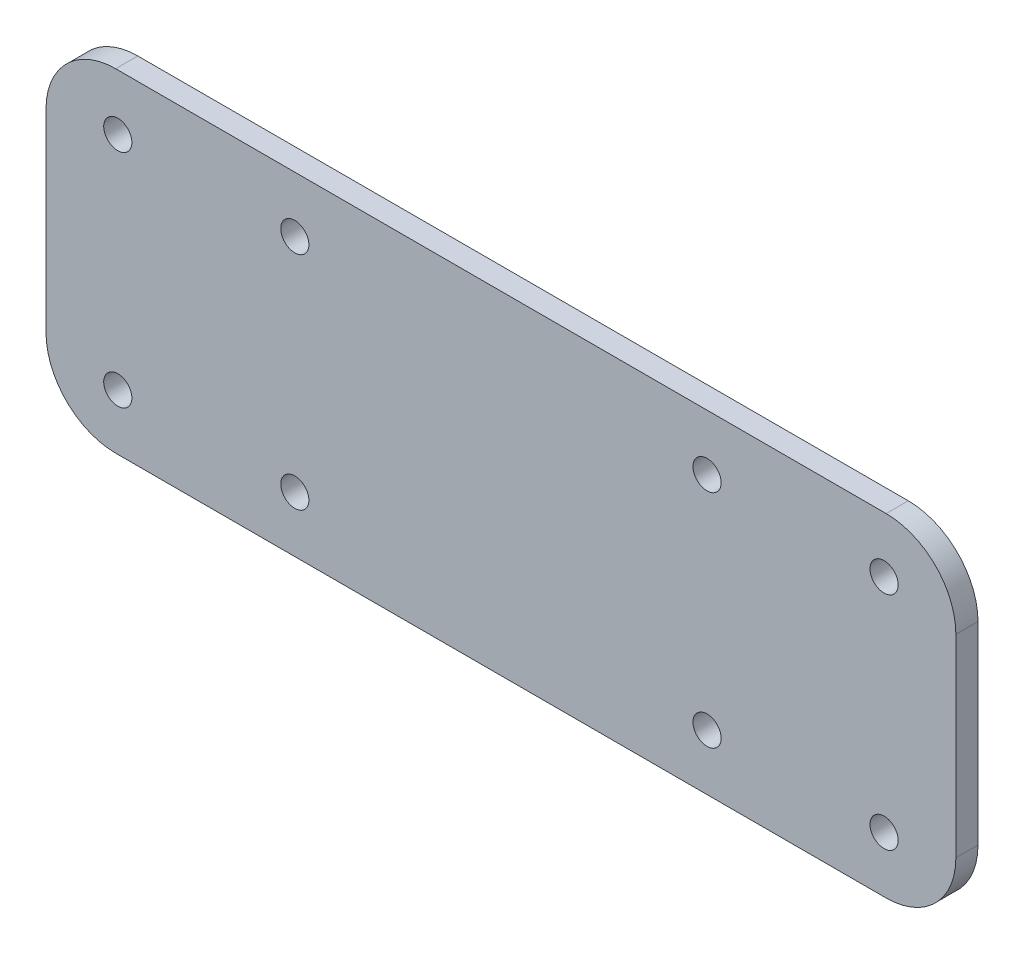
SolidWorks part; units mm, degrees
ref_plane "Front Plane" through (0, 0, 0) normal (0, 0, 1) x (1, 0, 0)
ref_plane "Top Plane" through (0, 0, 0) normal (0, 1, 0) x (1, 0, 0)
ref_plane "Right Plane" through (0, 0, 0) normal (1, 0, 0) x (0, 0, -1)
sketch "Sketch1" plane through (0, 0, 0) normal (0, 0, 1) x (1, 0, 0)
  line L0 (39.3854, -40.0501) -> (39.3854, -52.4111) construction
  line L1 (165.9345, -56.675) -> (165.9345, -42.05) construction
  line L2 (157.3152, -8.05) -> (165.9345, -16.6693)
  line L3 (157.3152, 245.3495) -> (165.9345, 253.9688)
  line L4 (39.3854, -40.0501) -> (39.3854, -52.4111)
  line L5 (165.9345, -56.675) -> (165.9345, -42.05)
  line L6 (165.9345, 245.3495) -> (39.3854, 245.3495)
  line L7 (165.9345, 279.3495) -> (165.9345, 245.3495)
  line L8 (39.3854, -52.4111) -> (165.9345, -56.675)
  line L9 (39.3854, 289.7105) -> (165.9345, 293.9745)
  line L10 (39.3854, -40.0501) -> (39.3854, -16.6693)
  line L11 (165.9345, -42.05) -> (165.9345, -16.6693)
  line L12 (157.3152, -8.05) -> (48.0047, -8.0501)
  line L13 (42.1433, 0) -> (42.1433, 237.2995) construction
  line L14 (42.1433, 118.6497) -> (215.0534, 118.6497) construction
  line L15 (165.9345, 293.9745) -> (165.9345, 279.3495)
  line L16 (39.3854, 277.3495) -> (39.3854, 245.3495)
  line L17 (39.3854, 277.3495) -> (39.3854, 289.7105)
  line L18 (102.66, -54.5431) -> (102.66, 291.8425) construction
  line L19 (102.66, 291.8425) -> (73.0854, -499321.8282) construction
  line L20 (39.3854, -16.6693) -> (89.96, 33.9052)
  line L21 (89.96, -8.05) -> (115.36, -8.05)
  line L22 (89.96, -8.05) -> (89.96, 245.3495)
  line L23 (89.96, 245.3495) -> (115.36, 245.3495)
  line L24 (115.36, -8.05) -> (115.36, 245.3495)
  line L25 (89.96, -8.05) -> (115.36, 245.3495) construction
  line L26 (89.96, 245.3495) -> (115.36, -8.05) construction
  line L27 (115.36, 33.9052) -> (157.3152, -8.05)
  line L28 (115.36, 203.3943) -> (157.3152, 245.3495)
  line L29 (39.3854, 253.9688) -> (89.96, 203.3943)
  arc A0 (157.6345, 249.9303) -> (157.6345, 253.9689) centre (157.6345, 251.9496) cw
  arc A1 (157.6345, 253.9689) -> (157.6345, 249.9303) centre (157.6345, 251.9496) cw
  arc A2 (73.0854, 249.9303) -> (73.0854, 253.9689) centre (73.0854, 251.9496) ccw
  arc A3 (73.0854, 253.9689) -> (73.0854, 249.9303) centre (73.0854, 251.9496) ccw
  arc A4 (73.0854, 249.9303) -> (73.0854, 253.9689) centre (73.0854, 251.9496) ccw
  arc A5 (73.0854, 253.9689) -> (73.0854, 249.9303) centre (73.0854, 251.9496) ccw
  arc A6 (47.6854, 249.9303) -> (47.6854, 253.9689) centre (47.6854, 251.9496) cw
  arc A7 (47.6854, 253.9689) -> (47.6854, 249.9303) centre (47.6854, 251.9496) cw
  arc A10 (47.6854, 281.6802) -> (47.6854, 285.7188) centre (47.6854, 283.6995) cw
  arc A11 (47.6854, 285.7188) -> (47.6854, 281.6802) centre (47.6854, 283.6995) cw
  arc A14 (157.6345, -48.4194) -> (157.6345, -44.3807) centre (157.6345, -46.4001) ccw
  arc A15 (157.6345, -44.3807) -> (157.6345, -48.4194) centre (157.6345, -46.4001) ccw
  arc A16 (157.6345, -48.4194) -> (157.6345, -44.3807) centre (157.6345, -46.4001) ccw
  arc A17 (157.6345, -44.3807) -> (157.6345, -48.4194) centre (157.6345, -46.4001) ccw
  arc A18 (73.0854, 281.6802) -> (73.0854, 285.7188) centre (73.0854, 283.6995) cw
  arc A19 (73.0854, 285.7188) -> (73.0854, 281.6802) centre (73.0854, 283.6995) cw
  arc A22 (157.6345, -16.6693) -> (157.6345, -12.6307) centre (157.6345, -14.65) ccw
  arc A23 (157.6345, -12.6307) -> (157.6345, -16.6693) centre (157.6345, -14.65) ccw
  arc A24 (157.6345, -16.6693) -> (157.6345, -12.6307) centre (157.6345, -14.65) ccw
  arc A25 (157.6345, -12.6307) -> (157.6345, -16.6693) centre (157.6345, -14.65) ccw
  arc A26 (73.0854, -16.6693) -> (73.0854, -12.6307) centre (73.0854, -14.65) ccw
  arc A27 (73.0854, -12.6307) -> (73.0854, -16.6693) centre (73.0854, -14.65) ccw
  arc A28 (73.0854, -16.6693) -> (73.0854, -12.6307) centre (73.0854, -14.65) ccw
  arc A29 (73.0854, -12.6307) -> (73.0854, -16.6693) centre (73.0854, -14.65) ccw
  arc A30 (73.0854, 249.9303) -> (73.0854, 253.9689) centre (73.0854, 251.9496) cw
  arc A31 (73.0854, 253.9689) -> (73.0854, 249.9303) centre (73.0854, 251.9496) cw
  arc A34 (157.6345, 249.9303) -> (157.6345, 253.9689) centre (157.6345, 251.9496) ccw
  arc A35 (157.6345, 253.9689) -> (157.6345, 249.9303) centre (157.6345, 251.9496) ccw
  arc A36 (157.6345, 249.9303) -> (157.6345, 253.9689) centre (157.6345, 251.9496) ccw
  arc A37 (157.6345, 253.9689) -> (157.6345, 249.9303) centre (157.6345, 251.9496) ccw
  arc A38 (47.6854, 249.9303) -> (47.6854, 253.9689) centre (47.6854, 251.9496) ccw
  arc A39 (47.6854, 253.9689) -> (47.6854, 249.9303) centre (47.6854, 251.9496) ccw
  arc A40 (47.6854, 249.9303) -> (47.6854, 253.9689) centre (47.6854, 251.9496) ccw
  arc A41 (47.6854, 253.9689) -> (47.6854, 249.9303) centre (47.6854, 251.9496) ccw
  arc A42 (73.0854, -48.4194) -> (73.0854, -44.3807) centre (73.0854, -46.4001) ccw
  arc A43 (73.0854, -44.3807) -> (73.0854, -48.4194) centre (73.0854, -46.4001) ccw
  arc A44 (73.0854, -48.4194) -> (73.0854, -44.3807) centre (73.0854, -46.4001) ccw
  arc A45 (73.0854, -44.3807) -> (73.0854, -48.4194) centre (73.0854, -46.4001) ccw
  arc A46 (132.2345, 249.9303) -> (132.2345, 253.9689) centre (132.2345, 251.9496) ccw
  arc A47 (132.2345, 253.9689) -> (132.2345, 249.9303) centre (132.2345, 251.9496) ccw
  arc A48 (132.2345, 249.9303) -> (132.2345, 253.9689) centre (132.2345, 251.9496) ccw
  arc A49 (132.2345, 253.9689) -> (132.2345, 249.9303) centre (132.2345, 251.9496) ccw
  arc A50 (47.6854, -48.4194) -> (47.6854, -44.3808) centre (47.6854, -46.4001) ccw
  arc A51 (47.6854, -44.3808) -> (47.6854, -48.4194) centre (47.6854, -46.4001) ccw
  arc A52 (47.6854, -48.4194) -> (47.6854, -44.3808) centre (47.6854, -46.4001) ccw
  arc A53 (47.6854, -44.3808) -> (47.6854, -48.4194) centre (47.6854, -46.4001) ccw
  arc A54 (47.6854, -16.6693) -> (47.6854, -12.6307) centre (47.6854, -14.65) ccw
  arc A55 (47.6854, -12.6307) -> (47.6854, -16.6693) centre (47.6854, -14.65) ccw
  arc A56 (47.6854, -16.6693) -> (47.6854, -12.6307) centre (47.6854, -14.65) ccw
  arc A57 (47.6854, -12.6307) -> (47.6854, -16.6693) centre (47.6854, -14.65) ccw
  arc A58 (157.6345, 281.6802) -> (157.6345, 285.7188) centre (157.6345, 283.6995) cw
  arc A59 (157.6345, 285.7188) -> (157.6345, 281.6802) centre (157.6345, 283.6995) cw
  arc A62 (132.2345, -16.6693) -> (132.2345, -12.6307) centre (132.2345, -14.65) ccw
  arc A63 (132.2345, -12.6307) -> (132.2345, -16.6693) centre (132.2345, -14.65) ccw
  arc A64 (132.2345, -16.6693) -> (132.2345, -12.6307) centre (132.2345, -14.65) ccw
  arc A65 (132.2345, -12.6307) -> (132.2345, -16.6693) centre (132.2345, -14.65) ccw
  arc A66 (132.2345, -48.4194) -> (132.2345, -44.3808) centre (132.2345, -46.4001) ccw
  arc A67 (132.2345, -44.3808) -> (132.2345, -48.4194) centre (132.2345, -46.4001) ccw
  arc A68 (132.2345, -48.4194) -> (132.2345, -44.3808) centre (132.2345, -46.4001) ccw
  arc A69 (132.2345, -44.3808) -> (132.2345, -48.4194) centre (132.2345, -46.4001) ccw
  point P62 (102.66, 118.6497)
  dimension "D3" = 0
  dimension "D2" = 25.4
  dimension "D1" = 0
  dimension "D4" = 0
  dimension "D5" = 0
  dimension "D6" = 0
  dimension "D7" = 0
  dimension "D9" = 0
  dimension "D10" = 0
  dimension "D11" = 0
  dimension "D12" = 0
  dimension "D13" = 0
  dimension "D14" = 0
extrude "Boss-Extrude1" add sketch "Sketch1" along normal blind 3.175 contours L20 L10 L4 L8 L5 L11 L2 L12 A69 A68 A65 A64 A57 A56 A53 A52 A45 A44 A29 A28 A25 A24 A17 A16 | L27 L24 L12 | L12 L24 L6 L22 | L12 L22 L20 | L16 L29 L6 L3 L7 L15 L9 L17 A49 A48 A5 A4 A0 A1 A6 A7 A10 A11 A18 A19 A58 A59 | L24 L28 L6 | L6 L29 L22
sketch "Sketch2" plane through (0, 0, 3.175) normal (0, 0, 1) x (1, 0, 0)
  line L0 (165.9345, -56.675) -> (165.9345, -16.6693) construction
  line L1 (39.3854, -52.4111) -> (84.3854, -52.4111)
  line L2 (39.3854, -52.4111) -> (39.3854, -7.4111)
  line L3 (39.3854, -7.4111) -> (84.3854, -7.4111)
  line L4 (84.3854, -52.4111) -> (84.3854, -7.4111)
  line L5 (165.9345, -52.4111) -> (120.9345, -52.4111)
  line L6 (165.9345, -52.4111) -> (165.9345, -7.4111)
  line L7 (165.9345, -7.4111) -> (120.9345, -7.4111)
  line L8 (120.9345, -52.4111) -> (120.9345, -7.4111)
  line L9 (89.96, 118.6497) -> (115.36, 118.6497) construction
  line L10 (89.96, 33.9052) -> (89.96, 203.3943) construction
  line L11 (115.36, 33.9052) -> (115.36, 203.3943) construction
  line L12 (165.9345, 289.7105) -> (120.9345, 289.7105)
  line L13 (39.3854, 289.7105) -> (84.3854, 289.7105)
  line L14 (84.3854, -52.4111) -> (120.9345, -52.4111)
  line L15 (84.3854, 289.7105) -> (120.9345, 289.7105)
  line M9 (39.3854, -52.4111) -> (165.9345, -56.675)
  line M10 (165.9345, -56.675) -> (165.9345, -16.6693)
  line M14 (165.9345, 253.9688) -> (165.9345, 293.9745)
  line M15 (165.9345, 293.9745) -> (39.3854, 289.7105)
  dimension "D1" = 45
extrude "Cut-Extrude1" cut sketch "Sketch2" against normal blind 10 contours L14 L1 L5 M9 M10 | L13 L15 L12 M14 M15
sketch "Sketch3" plane through (0, 0, 3.175) normal (0, 0, 1) x (1, 0, 0)
  line L25 (37.3854, -15.8409) -> (37.3854, -54.4111)
  line L26 (37.3854, -54.4111) -> (167.9345, -54.4111)
  line L27 (167.9345, -54.4111) -> (167.9345, -15.8409)
  line L28 (167.9345, -15.8409) -> (117.36, 34.7337)
  line L29 (117.36, 34.7337) -> (117.36, 202.5658)
  line L30 (117.36, 202.5658) -> (167.9345, 253.1404)
  line L31 (167.9345, 253.1404) -> (167.9345, 291.7105)
  line L32 (167.9345, 291.7105) -> (37.3854, 291.7105)
  line L33 (37.3854, 291.7105) -> (37.3854, 253.1404)
  line L34 (37.3854, 253.1404) -> (87.96, 202.5658)
  line L35 (87.96, 202.5658) -> (87.96, 34.7337)
  line L36 (87.96, 34.7337) -> (37.3854, -15.8409)
  line L37 (37.3854, -15.8409) -> (37.3854, -54.4111)
  line L38 (37.3854, -54.4111) -> (167.9345, -54.4111)
  line L39 (167.9345, -54.4111) -> (167.9345, -15.8409)
  line L40 (167.9345, -15.8409) -> (117.36, 34.7337)
  line L41 (117.36, 34.7337) -> (117.36, 202.5658)
  line L42 (117.36, 202.5658) -> (167.9345, 253.1404)
  line L43 (167.9345, 253.1404) -> (167.9345, 291.7105)
  line L44 (167.9345, 291.7105) -> (37.3854, 291.7105)
  line L45 (37.3854, 291.7105) -> (37.3854, 253.1404)
  line L46 (37.3854, 253.1404) -> (87.96, 202.5658)
  line L47 (87.96, 202.5658) -> (87.96, 34.7337)
  line L48 (87.96, 34.7337) -> (37.3854, -15.8409)
  circle A1 centre (132.2345, -46.4001) radius 2.0193
  circle A2 centre (132.2345, -46.4001) radius 2.0193
  circle A3 centre (132.2345, -14.65) radius 2.0193
  circle A4 centre (132.2345, -14.65) radius 2.0193
  circle A5 centre (47.6854, -14.65) radius 2.0193
  circle A6 centre (47.6854, -14.65) radius 2.0193
  circle A7 centre (47.6854, -46.4001) radius 2.0193
  circle A8 centre (47.6854, -46.4001) radius 2.0193
  circle A9 centre (73.0854, -46.4001) radius 2.0193
  circle A10 centre (73.0854, -46.4001) radius 2.0193
  circle A11 centre (73.0854, -14.65) radius 2.0193
  circle A12 centre (73.0854, -14.65) radius 2.0193
  circle A13 centre (157.6345, -14.65) radius 2.0193
  circle A14 centre (157.6345, -14.65) radius 2.0193
  circle A15 centre (157.6345, -46.4001) radius 2.0193
  circle A16 centre (157.6345, -46.4001) radius 2.0193
  circle A17 centre (132.2345, 251.9496) radius 2.0193
  circle A18 centre (132.2345, 251.9496) radius 2.0193
  circle A19 centre (73.0854, 251.9496) radius 2.0193
  circle A20 centre (73.0854, 251.9496) radius 2.0193
  circle A21 centre (157.6345, 251.9496) radius 2.0193
  circle A22 centre (157.6345, 251.9496) radius 2.0193
  circle A23 centre (47.6854, 251.9496) radius 2.0193
  circle A24 centre (47.6854, 251.9496) radius 2.0193
  circle A25 centre (47.6854, 283.6995) radius 2.0193
  circle A26 centre (47.6854, 283.6995) radius 2.0193
  circle A27 centre (73.0854, 283.6995) radius 2.0193
  circle A28 centre (73.0854, 283.6995) radius 2.0193
  circle A29 centre (157.6345, 283.6995) radius 2.0193
  circle A30 centre (157.6345, 283.6995) radius 2.0193
  dimension "D1" = 2
  dimension "D2" = 0
  dimension "D3" = 0
  dimension "D4" = 0
  dimension "D5" = 0
  dimension "D6" = 0
  dimension "D7" = 0
  dimension "D8" = 0
  dimension "D9" = 0
  dimension "D10" = 0
  dimension "D11" = 0
  dimension "D12" = 0
  dimension "D13" = 0
  dimension "D14" = 0
  dimension "D15" = 0
  dimension "D16" = 0
extrude "Boss-Extrude2" add sketch "Sketch3" against normal up to surface (3.175 mm away) up to face at (159.6538, 283.6995, 0)
fillet "Fillet1" radius 10 8 edges at (37.3854, 253.1404, 1.5875) (37.3854, 291.7105, 1.5875) (167.9345, 291.7105, 1.5875) (167.9345, 253.1404, 1.5875) (37.3854, -15.8409, 1.5875) (167.9345, -15.8409, 1.5875) (167.9345, -54.4111, 1.5875) (37.3854, -54.4111, 1.5875)
fillet "Fillet2" radius 50 4 edges at (87.96, 34.7337, 1.5875) (117.36, 34.7337, 1.5875) (87.96, 202.5658, 1.5875) (117.36, 202.5658, 1.5875)
sketch "Sketch4" plane through (0, 0, 3.175) normal (0, 0, 1) x (1, 0, 0)
  circle A0 centre (132.2345, 283.6995) radius 2.02
  dimension "D1" = 4.04
extrude "Cut-Extrude2" cut sketch "Sketch4" against normal blind 10
sketch "Sketch5" plane through (0, 0, 3.175) normal (0, 0, 1) x (1, 0, 0)
  line L0 (47.6854, -46.4001) -> (47.6854, -30.525)
  line L1 (47.6854, -30.525) -> (167.9345, -30.525)
  line L2 (47.6854, -30.525) -> (37.3854, -30.525)
  line L3 (47.3854, -6.639) -> (157.9345, -6.639)
  line L15 (37.3854, 281.7105) -> (37.3854, 257.2826)
  line L16 (40.3143, 250.2115) -> (73.3153, 217.2105)
  line L17 (87.96, 181.8552) -> (87.96, 55.4443)
  line L18 (73.3153, 20.089) -> (40.3143, -12.912)
  line L19 (37.3854, -19.9831) -> (37.3854, -44.4111)
  line L20 (47.3854, -54.4111) -> (157.9345, -54.4111)
  line L21 (167.9345, -44.4111) -> (167.9345, -19.9831)
  line L22 (165.0056, -12.912) -> (132.0046, 20.089)
  line L23 (117.36, 55.4443) -> (117.36, 181.8552)
  line L24 (132.0046, 217.2105) -> (165.0056, 250.2115)
  line L25 (167.9345, 257.2826) -> (167.9345, 281.7105)
  line L26 (157.9345, 291.7105) -> (47.3854, 291.7105)
  line L31 (37.3854, -16.639) -> (37.3854, -44.4111)
  line L32 (47.3854, -54.4111) -> (157.9345, -54.4111)
  line L33 (167.9345, -44.4111) -> (167.9345, -16.639)
  arc A0 (157.9345, -6.639) -> (167.9345, -16.639) centre (157.9345, -16.639) cw
  circle A1 centre (157.6345, -14.65) radius 2.0193
  circle A2 centre (73.0854, -14.65) radius 2.0193
  circle A3 centre (47.6854, -14.65) radius 2.0193
  circle A4 centre (132.2345, -14.65) radius 2.0193
  arc A5 (37.3854, -16.639) -> (47.3854, -6.639) centre (47.3854, -16.639) cw
  arc A12 (37.3854, 257.2826) -> (40.3143, 250.2115) centre (47.3854, 257.2826) ccw
  arc A13 (87.96, 181.8552) -> (73.3153, 217.2105) centre (37.96, 181.8552) ccw
  arc A14 (73.3153, 20.089) -> (87.96, 55.4443) centre (37.96, 55.4443) ccw
  arc A15 (40.3143, -12.912) -> (37.3854, -19.9831) centre (47.3854, -19.9831) ccw
  arc A16 (37.3854, -44.4111) -> (47.3854, -54.4111) centre (47.3854, -44.4111) ccw
  arc A17 (157.9345, -54.4111) -> (167.9345, -44.4111) centre (157.9345, -44.4111) ccw
  arc A18 (167.9345, -19.9831) -> (165.0056, -12.912) centre (157.9345, -19.9831) ccw
  arc A19 (117.36, 55.4443) -> (132.0046, 20.089) centre (167.36, 55.4443) ccw
  arc A20 (132.0046, 217.2105) -> (117.36, 181.8552) centre (167.36, 181.8552) ccw
  arc A21 (165.0056, 250.2115) -> (167.9345, 257.2826) centre (157.9345, 257.2826) ccw
  arc A22 (167.9345, 281.7105) -> (157.9345, 291.7105) centre (157.9345, 281.7105) ccw
  arc A23 (47.3854, 291.7105) -> (37.3854, 281.7105) centre (47.3854, 281.7105) ccw
  arc A28 (37.3854, -44.4111) -> (47.3854, -54.4111) centre (47.3854, -44.4111) ccw
  arc A29 (157.9345, -54.4111) -> (167.9345, -44.4111) centre (157.9345, -44.4111) ccw
  circle A37 centre (132.2345, -46.4001) radius 2.0193
  circle A38 centre (132.2345, -46.4001) radius 2.0193
  circle A39 centre (132.2345, -14.65) radius 2.0193
  circle A40 centre (132.2345, -14.65) radius 2.0193
  circle A43 centre (47.6854, -46.4001) radius 2.0193
  circle A44 centre (47.6854, -46.4001) radius 2.0193
  circle A45 centre (73.0854, -46.4001) radius 2.0193
  circle A46 centre (73.0854, -46.4001) radius 2.0193
  circle A49 centre (157.6345, -14.65) radius 2.0193
  circle A50 centre (157.6345, -14.65) radius 2.0193
  circle A51 centre (157.6345, -46.4001) radius 2.0193
  circle A52 centre (157.6345, -46.4001) radius 2.0193
  dimension "D1" = 0
  dimension "D2" = 0
  dimension "D3" = 0
  dimension "D5" = 0
  dimension "D6" = 0
  dimension "D8" = 0
  dimension "D9" = 0
extrude "Boss-Extrude3" add sketch "Sketch5" along normal blind 3.175
sketch "Sketch6" plane through (37.3854, 0, 0) normal (-1, 0, 0) x (0, 0, 1)
  line L1 (0, -54.4111) -> (3.175, -54.4111)
  line L2 (0, -54.4111) -> (0, 291.7105)
  line L3 (0, 291.7105) -> (3.175, 291.7105)
  line L4 (3.175, -54.4111) -> (3.175, 291.7105)
extrude "Cut-Extrude3" cut sketch "Sketch6" against normal through all
